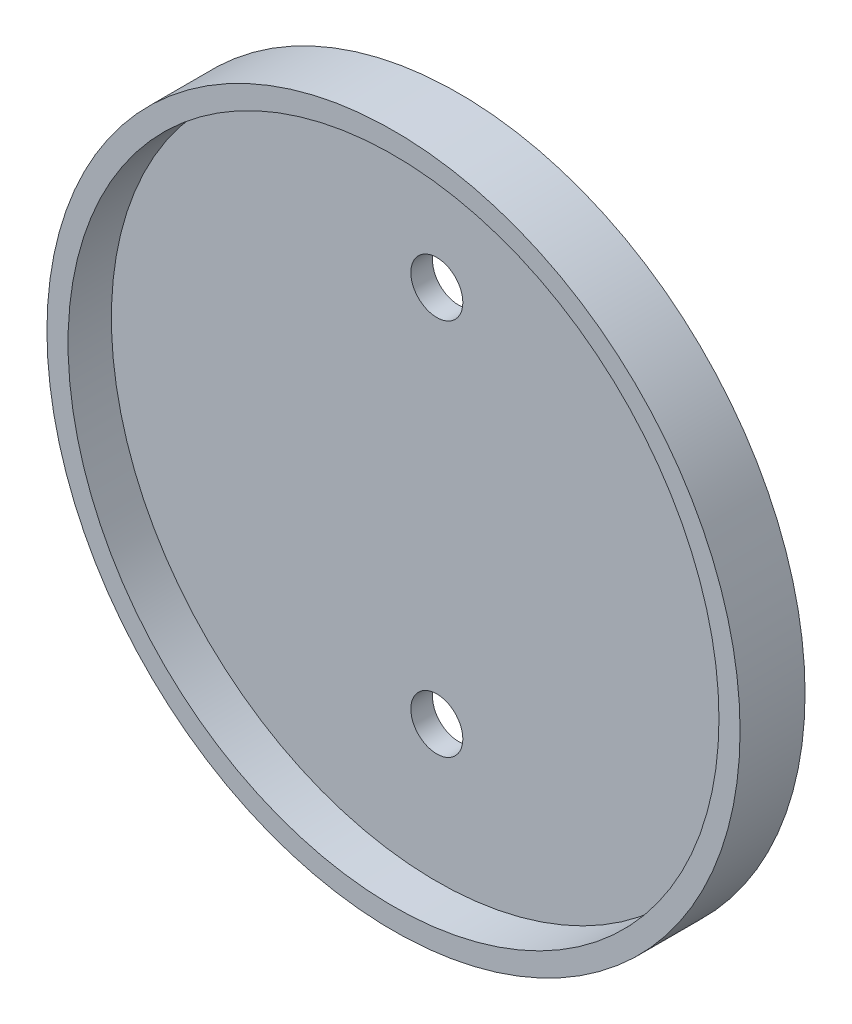
SolidWorks part; units mm, degrees
material "ABS"
ref_plane "X-Y Datum" through (0, 0, 0) normal (0, 0, 1) x (1, 0, 0)
ref_plane "X-Z Datum" through (0, 0, 0) normal (0, 1, 0) x (1, 0, 0)
ref_plane "Y-Z Datum" through (0, 0, 0) normal (1, 0, 0) x (0, 0, -1)
sketch "Sketch1" plane through (0, 0, 0) normal (0, 0, 1) x (1, 0, 0)
  circle A0 centre (0, 0) radius 32
  dimension "D1" = 64
extrude "Boss-Extrude1" add sketch "Sketch1" along normal mid plane 2
sketch "Sketch2" plane through (0, 0, 1) normal (0, 0, 1) x (1, 0, 0)
  circle A3 centre (0, 0) radius 30.05
  circle A4 centre (0, 0) radius 32
  circle A5 centre (0, 0) radius 32
  dimension "D1" = 60.1
  dimension "D2" = 0
extrude "Boss-Extrude2" add sketch "Sketch2" along normal blind 4
hole_wizard "M4 Clearance Hole1" positions "Sketch3" profile "Sketch4" hole size "M4" standard "ANSI Metric" end condition up to next
sketch "Sketch3" plane through (0, 0, -1) normal (0, 0, -1) x (-1, 0, 0)
  line L0 (0, -32) -> (0, 32) construction
  line L1 (0, 0) -> (-32, 0) construction
  circle A0 centre (0, 0) radius 32 construction
  point P7 (0, -17.4498)
  point P9 (0, 17.4498)
  dimension "D1" = 34.8996
sketch "Sketch4" plane through (0, 17.4498, -1) normal (1, 0, 0) x (0, 1, 0)
  line L0 (0, 0) -> (0, 2)
  line L1 (0, 2) -> (2.4, 2)
  line L2 (2.4, 2) -> (2.4, 0)
  line L5 (2.4, 0) -> (0, 0)
  line L11 (0, -6.35) -> (0, 107.95) construction
  dimension "Thru Hole Dia." = 4.8
  dimension "Thru Hole Depth" = 2
